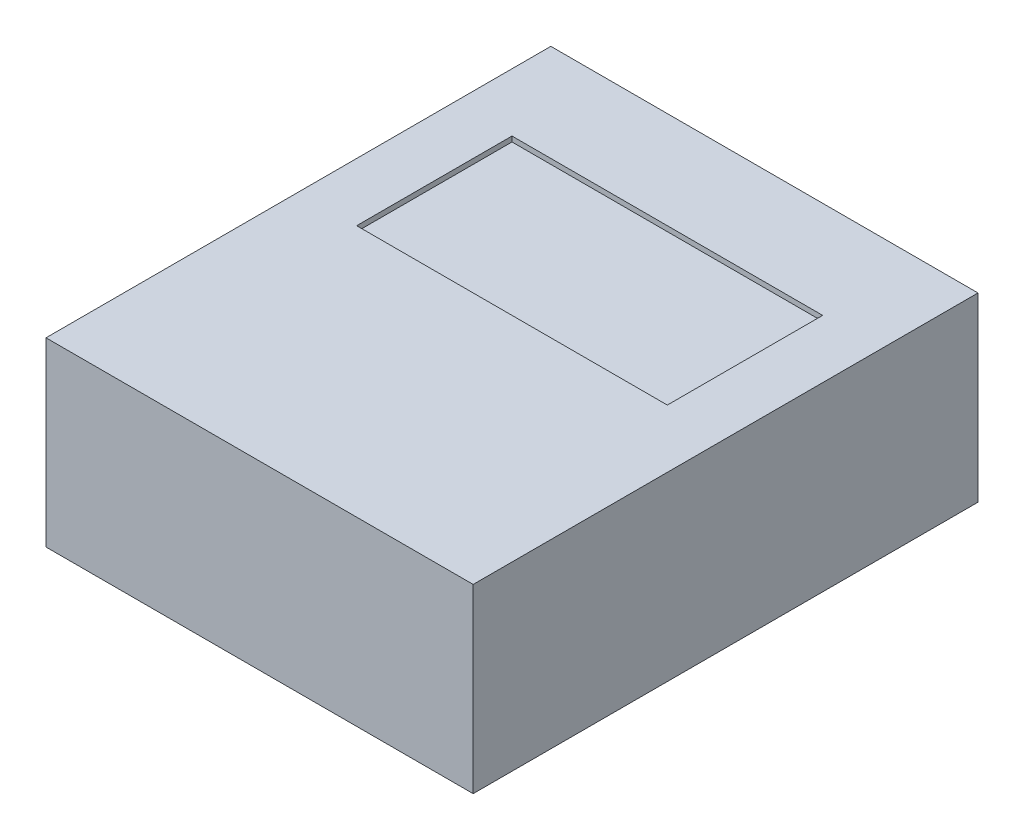
SolidWorks part; units mm, degrees
ref_plane "Plan de face" through (0, 0, 0) normal (0, 0, 1) x (1, 0, 0)
ref_plane "Plan de dessus" through (0, 0, 0) normal (0, 1, 0) x (1, 0, 0)
ref_plane "Plan de droite" through (0, 0, 0) normal (1, 0, 0) x (0, 0, -1)
sketch "Esquisse1" plane through (0, 0, 0) normal (0, 1, 0) x (1, 0, 0)
  line L1 (-82.5, -97.5) -> (82.5, -97.5)
  line L2 (-82.5, -97.5) -> (-82.5, 97.5)
  line L3 (-82.5, 97.5) -> (82.5, 97.5)
  line L4 (82.5, -97.5) -> (82.5, 97.5)
  line L5 (-82.5, -97.5) -> (82.5, 97.5) construction
  line L6 (-82.5, 97.5) -> (82.5, -97.5) construction
  point P0 (0, 0)
  dimension "D1" = 165
  dimension "D2" = 195
extrude "Boss.-Extru.1" add sketch "Esquisse1" along normal mid plane 70
sketch "Esquisse4" plane through (0, 35, 0) normal (0, 1, 0) x (1, 0, 0)
  line L1 (0, -38.5) -> (0, 38.5) construction
  line L2 (-60, 0) -> (60, 0)
  line L3 (-60, 0) -> (-60, 60)
  line L4 (-60, 60) -> (60, 60)
  line L5 (60, 0) -> (60, 60)
  line L6 (-60, 0) -> (60, 60) construction
  line L7 (-60, 60) -> (60, 0) construction
  line L8 (-38.5, 0) -> (38.5, 0) construction
  point P0 (0, 0)
  point P2 (0, 30)
  dimension "D1" = 60
  dimension "D2" = 120
  dimension "D3" = 30
extrude "Enlèv. mat.-Extru.1" cut sketch "Esquisse4" against normal blind 2
